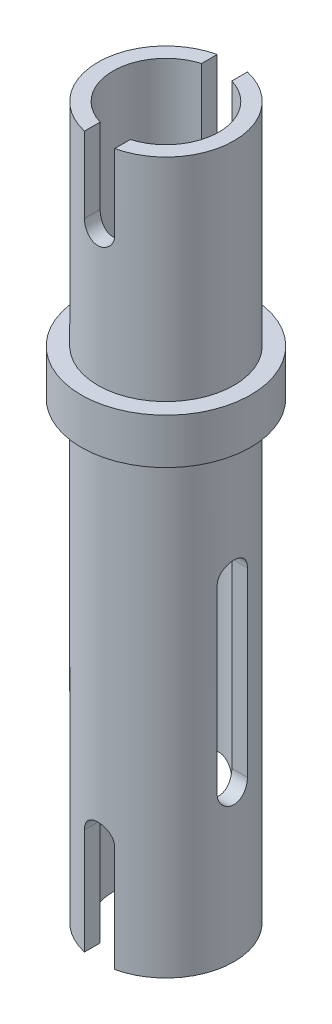
SolidWorks part; units mm, degrees
ref_plane "Front Plane" through (0, 0, 0) normal (0, 0, 1) x (1, 0, 0)
ref_plane "Top Plane" through (0, 0, 0) normal (0, 1, 0) x (1, 0, 0)
ref_plane "Right Plane" through (0, 0, 0) normal (1, 0, 0) x (0, 0, -1)
sketch "Sketch1" plane through (0, 0, 0) normal (0, 1, 0) x (1, 0, 0)
  circle A0 centre (0, 0) radius 2.8
  dimension "D1" = 5.6
extrude "Boss-Extrude1" add sketch "Sketch1" along normal blind 1.5
sketch "Sketch2" plane through (0, 1.5, 0) normal (0, 1, 0) x (1, 0, 0)
  circle A0 centre (0, 0) radius 2.25
  dimension "D1" = 4.5
extrude "Boss-Extrude2" add sketch "Sketch2" along normal blind 7
sketch "Sketch3" plane through (0, 0, 0) normal (0, -1, 0) x (1, 0, 0)
  circle A0 centre (0, 0) radius 2.25
  dimension "D1" = 4.5
extrude "Boss-Extrude3" add sketch "Sketch3" along normal blind 15
ref_plane "Plane1" through (0, 0, 10) normal (0, 0, 1) x (1, 0, 0)
sketch "Sketch4" plane through (0, 0, 10) normal (0, 0, 1) x (1, 0, 0)
  line L0 (0, 1.5) -> (0, 6) construction
  line L1 (2.8, 1.5) -> (-2.8, 1.5) construction
  line L2 (0, 6) -> (0, 8.5) construction
  line L3 (2.25, 8.5) -> (-2.25, 8.5) construction
  line L4 (-0.5, 6) -> (-0.5, 8.5)
  line L5 (0.5, 6) -> (0.5, 8.5)
  line L6 (0, 0) -> (0, -11.5) construction
  line L7 (0, -11.5) -> (0, -15) construction
  line L8 (-2.25, -15) -> (2.25, -15) construction
  line L9 (0.5, -11.5) -> (0.5, -15)
  line L10 (-0.5, -11.5) -> (-0.5, -15)
  arc A0 (-0.5, 6) -> (0.5, 6) centre (0, 6) ccw
  arc A1 (0.5, 8.5) -> (-0.5, 8.5) centre (0, 8.5) ccw
  arc A2 (0.5, -11.5) -> (-0.5, -11.5) centre (0, -11.5) ccw
  arc A3 (-0.5, -15) -> (0.5, -15) centre (0, -15) ccw
  point P5 (0, 7.25)
  point P15 (0, -13.25)
extrude "Cut-Extrude1" cut sketch "Sketch4" against normal through all
ref_plane "Plane2" through (10, 0, 0) normal (1, 0, 0) x (0, 0, -1)
sketch "Sketch5" plane through (10, 0, 0) normal (1, 0, 0) x (0, 0, -1)
  line L0 (0, 0) -> (0, -4) construction
  line L1 (0, -4) -> (0, -10) construction
  line L2 (0.5, -4) -> (0.5, -10)
  line L3 (-0.5, -4) -> (-0.5, -10)
  arc A0 (0.5, -4) -> (-0.5, -4) centre (0, -4) ccw
  arc A1 (-0.5, -10) -> (0.5, -10) centre (0, -10) ccw
  point P3 (0, -7)
  dimension "D1" = 4
extrude "Cut-Extrude2" cut sketch "Sketch5" against normal through all
ref_plane "Plane3" through (0, 10, 0) normal (0, 1, 0) x (1, 0, 0)
sketch "Sketch6" plane through (0, 10, 0) normal (0, 1, 0) x (1, 0, 0)
  circle A0 centre (0, 0) radius 1.75
  dimension "D1" = 3.5
extrude "Cut-Extrude3" cut sketch "Sketch6" against normal through all
